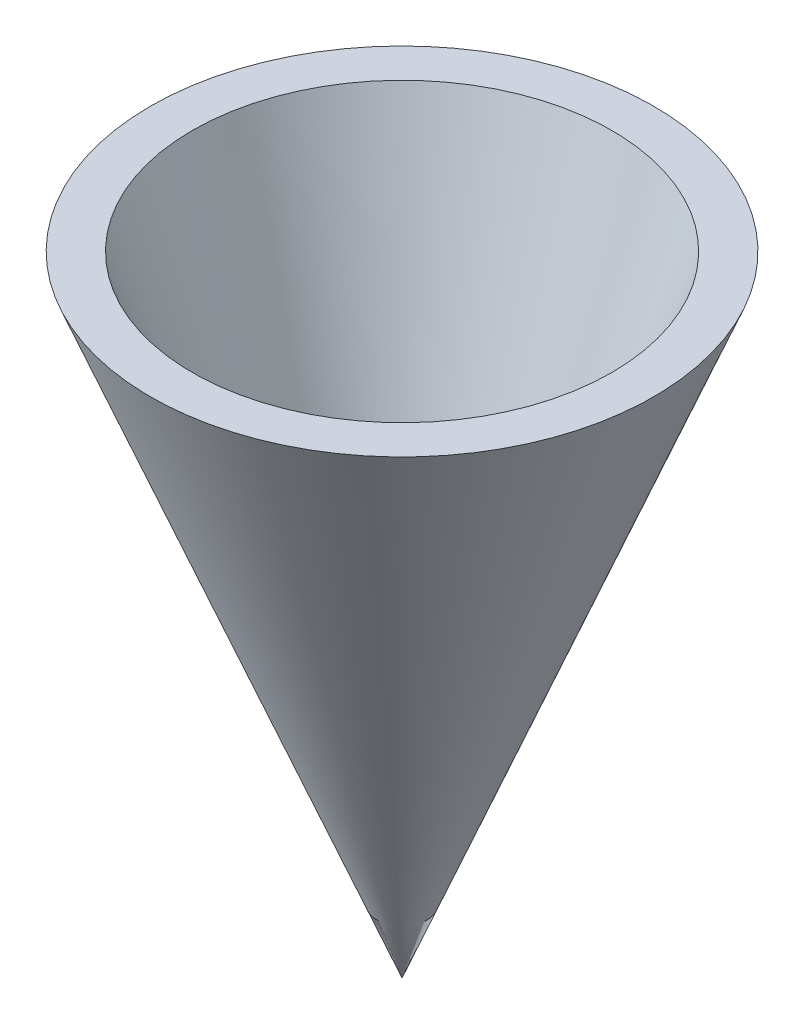
SolidWorks part; units mm, degrees
ref_plane "Alzado" through (0, 0, 0) normal (0, 0, 1) x (1, 0, 0)
ref_plane "Planta" through (0, 0, 0) normal (0, 1, 0) x (1, 0, 0)
ref_plane "Vista lateral" through (0, 0, 0) normal (1, 0, 0) x (0, 0, -1)
sketch "Croquis2" plane through (0, 0, 0) normal (0, 0, 1) x (1, 0, 0)
  line L0 (-10, 0) -> (-12, 0)
  line L1 (0, 0) -> (0, -20.9297) construction
  line L2 (-10, 0) -> (-3.0234, -20.9297)
  line L3 (-12, 0) -> (0, -30)
  line L4 (-3.0234, -20.9297) -> (0, -25.4648)
  line L5 (0, -25.4648) -> (0, -30)
  line L6 (0, -25.4648) -> (0, -30) construction
  dimension "D1" = 30
revolve "Revolución1" add sketch "Croquis2" angle 360 about L1
